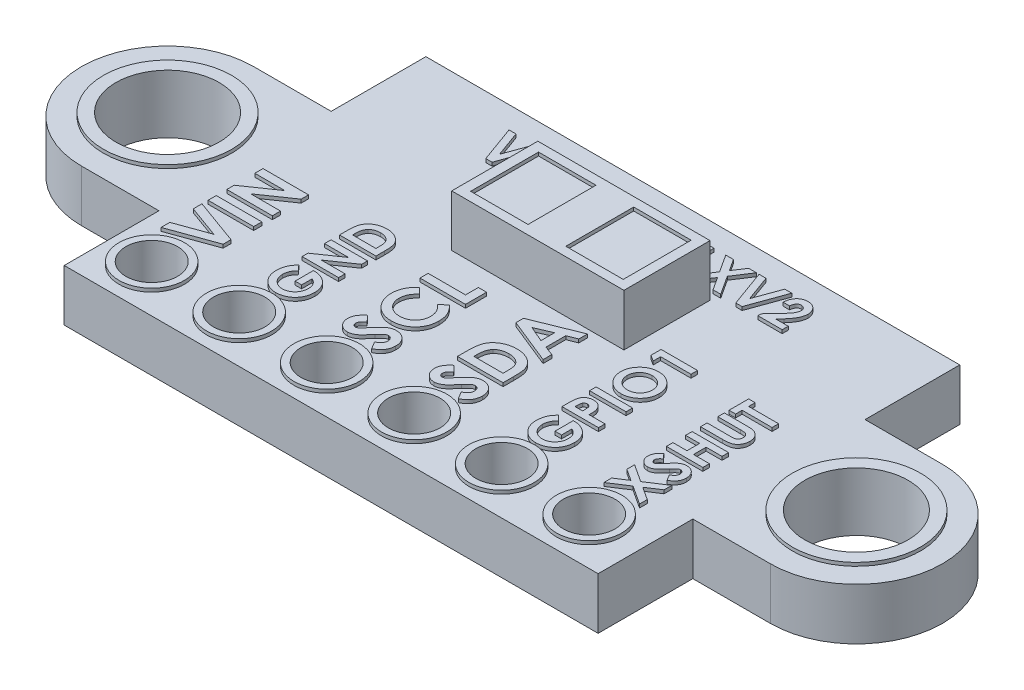
SolidWorks part; units mm, degrees
ref_plane "Ön Düzlem" through (0, 0, 0) normal (0, 0, 1) x (1, 0, 0)
ref_plane "Üst Düzlem" through (0, 0, 0) normal (0, 1, 0) x (1, 0, 0)
ref_plane "Sağ Düzlem" through (0, 0, 0) normal (1, 0, 0) x (0, 0, -1)
sketch "Çizim1" plane through (0, 0, 0) normal (0, 1, 0) x (1, 0, 0)
  line L0 (-10, 0) -> (10, 0) construction
  line L1 (-7.75, -5.25) -> (7.75, -5.25)
  line L2 (-7.75, -5.25) -> (-7.75, -2.5)
  line L3 (-7.75, 5.25) -> (7.75, 5.25)
  line L4 (7.75, -5.25) -> (7.75, -2.5)
  line L5 (-7.75, -5.25) -> (7.75, 5.25) construction
  line L6 (-7.75, 5.25) -> (7.75, -5.25) construction
  line L7 (-10, 2.5) -> (-7.75, 2.5)
  line L8 (-10, -2.5) -> (-7.75, -2.5)
  line L9 (10, -2.5) -> (7.75, -2.5)
  line L10 (10, 2.5) -> (7.75, 2.5)
  line L11 (-7.75, 2.5) -> (-7.75, 5.25)
  line L12 (7.75, 2.5) -> (7.75, 5.25)
  circle A0 centre (-10, 0) radius 1.5
  circle A1 centre (10, 0) radius 1.5
  arc A3 (-10, 2.5) -> (-10, -2.5) centre (-10, 0) ccw
  arc A4 (10, -2.5) -> (10, 2.5) centre (10, 0) ccw
  circle A5 centre (-10, 0) radius 2.5 construction
  circle A6 centre (10, 0) radius 2.5 construction
  point P0 (0, 0)
  dimension "D3" = 1
  dimension "D1" = 15.5
  dimension "D2" = 10.5
extrude "Yükseklik-Ekstrüzyon1" add sketch "Çizim1" along normal blind 1.5
sketch "Çizim2" plane through (0, 1.5, 0) normal (0, 1, 0) x (1, 0, 0)
  line L0 (0, 5.25) -> (0, 2) construction
  line L1 (7.75, 5.25) -> (-7.75, 5.25) construction
  line L3 (-2.5, 0.75) -> (2.5, 0.75)
  line L4 (-2.5, 0.75) -> (-2.5, 3.25)
  line L5 (-2.5, 3.25) -> (2.5, 3.25)
  line L6 (2.5, 0.75) -> (2.5, 3.25)
  line L7 (-2.5, 0.75) -> (2.5, 3.25) construction
  line L8 (-2.5, 3.25) -> (2.5, 0.75) construction
extrude "Yükseklik-Ekstrüzyon2" add sketch "Çizim2" along normal blind 1.5
sketch "Çizim3" plane through (0, 3, 0) normal (0, 1, 0) x (1, 0, 0)
  line L3 (0, 3.25) -> (0, 0.75) construction
  line L7 (2.5, 3.25) -> (-2.5, 3.25) construction
  line L12 (-2.5, 0.75) -> (2.5, 0.75) construction
  line L13 (0, 2) -> (-2.5, 2) construction
  line L14 (-2.5, 3.25) -> (-2.5, 0.75) construction
  line L15 (2.2157, 1.014) -> (0.548, 2.986) construction
  line L16 (-2.2157, 2.986) -> (-0.548, 2.986)
  line L17 (-2.2157, 2.986) -> (-2.2157, 1.014)
  line L18 (-2.2157, 1.014) -> (-0.548, 1.014)
  line L19 (-0.548, 2.986) -> (-0.548, 1.014)
  line L20 (-2.2157, 2.986) -> (-0.548, 1.014) construction
  line L21 (-2.2157, 1.014) -> (-0.548, 2.986) construction
  line L22 (2.2157, 2.986) -> (0.548, 1.014) construction
  line L23 (0.548, 2.986) -> (0.548, 1.014)
  line L24 (2.2157, 1.014) -> (0.548, 1.014)
  line L25 (2.2157, 2.986) -> (2.2157, 1.014)
  line L26 (2.2157, 2.986) -> (0.548, 2.986)
  point P10 (-1.3818, 2)
  point P19 (1.3818, 2)
extrude "Kes-Ekstrüzyon1" cut sketch "Çizim3" against normal blind 0.1
sketch "Çizim4" plane through (0, 1.5, 0) normal (0, 1, 0) x (1, 0, 0)
  line L0 (0, 0) -> (0, -1.1087) construction
  circle A0 centre (10, 0) radius 1.8604
  circle A1 centre (10, 0) radius 1.5 construction
  circle A2 centre (10, 0) radius 1.5
  circle A3 centre (-10, 0) radius 1.5
  circle A4 centre (-10, 0) radius 1.8604
extrude "Yükseklik-Ekstrüzyon3" add sketch "Çizim4" along normal blind 0.1 and the other way blind 1.6
sketch "Çizim5" plane through (0, 1.5, 0) normal (0, 1, 0) x (1, 0, 0)
  line L0 (-7.75, -5.25) -> (-7.75, -3.98) construction
  line L1 (-7.75, -2.5) -> (-7.75, -5.25) construction
  line L2 (-7.75, -3.98) -> (-6.48, -3.98) construction
  circle A0 centre (-6.48, -3.98) radius 0.75
  circle A1 centre (-3.94, -3.98) radius 0.75
  circle A2 centre (-1.4, -3.98) radius 0.75
  circle A3 centre (1.14, -3.98) radius 0.75
  circle A4 centre (3.68, -3.98) radius 0.75
  circle A5 centre (6.22, -3.98) radius 0.75
  dimension "D1" = 6
extrude "Kes-Ekstrüzyon2" cut sketch "Çizim5" against normal blind 3.1
sketch "Çizim6" plane through (0, 1.5, 0) normal (0, 1, 0) x (1, 0, 0)
  circle A0 centre (-6.48, -3.98) radius 0.75 construction
  circle A1 centre (-6.48, -3.98) radius 0.75
  circle A2 centre (-6.48, -3.98) radius 0.95
  dimension "D1" = 0.2
extrude "Yükseklik-Ekstrüzyon4" add sketch "Çizim6" along normal blind 0.1 and the other way blind 1.6
pattern_linear "LÇoğaltma1" count 6 spacing 2.54 along (1, 0, 0) of "Yükseklik-Ekstrüzyon4"
sketch "Çizim7" plane through (0, 1.5, 0) normal (0, 1, 0) x (1, 0, 0)
  line L0 (-3.3625, -3.03) -> (-3.3625, 1.2923) construction
  line L1 (-5.8779, -3.03) -> (-5.8779, 1.2923) construction
  line L2 (-0.8471, -3.03) -> (-0.8471, 1.2923) construction
  line L3 (1.6682, -3.03) -> (1.6682, 1.2923) construction
  line L4 (4.1836, -3.03) -> (4.1836, 1.2923) construction
  line L5 (6.6989, -3.03) -> (6.6989, 1.2923) construction
  text T0 "VIN" font "Century Gothic" height in points 5
  text T1 "GND" font "Century Gothic" height in points 4
  text T2 "<b>SCL</b>" font "Century Gothic" height in points 5
  text T3 "SDA" font "Century Gothic" height in points 5
  text T4 "GPIO1" font "Century Gothic" height in points 4
  text T5 "<b>XSHUT</b>" font "Century Gothic" height in points 4
  dimension "D1" = 6
extrude "Yükseklik-Ekstrüzyon5" add sketch "Çizim7" along normal blind 0.1
sketch "Çizim8" plane through (0, 1.5, 0) normal (0, 1, 0) x (1, 0, 0)
  line L0 (-5.0829, 3.4564) -> (4.9171, 3.4564) construction
  line L1 (0, 0) -> (0, 5.25) construction
  line L2 (7.75, 5.25) -> (-7.75, 5.25) construction
  text T0 "VL53L0/1XV2" font "Century Gothic" height in points 4
extrude "Yükseklik-Ekstrüzyon6" add sketch "Çizim8" along normal blind 0.1
sketch "Çizim9" plane through (0, 0, 0) normal (0, -1, 0) x (1, 0, 0)
  line L0 (-1.7136, -3.2806) -> (-1.2276, -3.2806)
  line L1 (2.6326, 0.7695) -> (3.9286, 0.7695)
  line L2 (2.6326, 0.7695) -> (2.6326, -2.0656)
  line L3 (2.6326, -2.0656) -> (3.9286, -2.0656)
  line L4 (3.9286, 0.7695) -> (3.9286, -2.0656)
  line L5 (2.6326, 0.7695) -> (3.9286, -2.0656) construction
  line L6 (2.6326, -2.0656) -> (3.9286, 0.7695) construction
  line L7 (-2.7136, -3.2806) -> (-2.2276, -3.2806)
  line L8 (-2.7136, -3.2806) -> (-2.7136, -4.3336)
  line L9 (-2.7136, -4.3336) -> (-2.2276, -4.3336)
  line L10 (-2.2276, -3.2806) -> (-2.2276, -4.3336)
  line L11 (-2.7136, -3.2806) -> (-2.2276, -4.3336) construction
  line L12 (-2.7136, -4.3336) -> (-2.2276, -3.2806) construction
  line L17 (-1.7136, -3.2806) -> (-1.7136, -4.3336)
  line L18 (-1.7136, -4.3336) -> (-1.2276, -4.3336)
  line L23 (-1.2276, -3.2806) -> (-1.2276, -4.3336)
  line L24 (-1.7136, -3.2806) -> (-1.2276, -4.3336) construction
  line L25 (-1.7136, -4.3336) -> (-1.2276, -3.2806) construction
  line L26 (-0.7136, -3.2806) -> (-0.2276, -3.2806)
  line L27 (-0.7136, -3.2806) -> (-0.7136, -4.3336)
  line L28 (-0.7136, -4.3336) -> (-0.2276, -4.3336)
  line L29 (-0.2276, -3.2806) -> (-0.2276, -4.3336)
  line L30 (-0.7136, -3.2806) -> (-0.2276, -4.3336) construction
  line L31 (-0.7136, -4.3336) -> (-0.2276, -3.2806) construction
  line L32 (-5.7336, 1.0241) -> (-5.2741, 1.0241)
  line L33 (-6.7336, 1.0241) -> (-6.2741, 1.0241)
  line L34 (-6.7336, 1.0241) -> (-6.7336, -0.1705)
  line L35 (-6.7336, -0.1705) -> (-6.2741, -0.1705)
  line L36 (-6.2741, 1.0241) -> (-6.2741, -0.1705)
  line L37 (-6.7336, 1.0241) -> (-6.2741, -0.1705) construction
  line L38 (-6.7336, -0.1705) -> (-6.2741, 1.0241) construction
  line L39 (-5.7336, 1.0241) -> (-5.7336, -0.1705)
  line L40 (-5.7336, -0.1705) -> (-5.2741, -0.1705)
  line L41 (-5.2741, 1.0241) -> (-5.2741, -0.1705)
  line L42 (-5.7336, 1.0241) -> (-5.2741, -0.1705) construction
  line L43 (-5.7336, -0.1705) -> (-5.2741, 1.0241) construction
  point P0 (3.2806, -0.648)
  point P5 (-2.4706, -3.8071)
  point P10 (-6.5038, 0.4268)
  point P11 (-1.4706, -3.8071)
  point P16 (-0.4706, -3.8071)
  point P27 (-5.5038, 0.4268)
  dimension "D1" = 3
  dimension "D2" = 2
extrude "Yükseklik-Ekstrüzyon7" add sketch "Çizim9" along normal blind 1
sketch "Çizim10" plane through (0, -1, 0) normal (0, -1, 0) x (1, 0, 0)
  line L0 (-0.2276, -4.3336) -> (-0.2276, -3.2806) construction
  line L1 (-0.2276, -3.2806) -> (-0.7136, -3.2806) construction
  line L2 (-0.7136, -3.2806) -> (-0.7136, -4.3336) construction
  line L3 (-0.7136, -4.3336) -> (-0.2276, -4.3336) construction
  line L4 (-5.2741, -0.1705) -> (-5.2741, 1.0241)
  line L5 (-5.2741, 1.0241) -> (-5.7336, 1.0241)
  line L6 (-5.7336, 1.0241) -> (-5.7336, -0.1705)
  line L7 (-5.7336, -0.1705) -> (-5.2741, -0.1705)
  line L8 (-5.2741, -0.1705) -> (-5.2741, 1.0241)
  line L9 (-5.2741, 1.0241) -> (-5.7336, 1.0241)
  line L10 (-5.7336, 1.0241) -> (-5.7336, -0.1705)
  line L11 (-5.7336, -0.1705) -> (-5.2741, -0.1705)
  line L12 (-6.2741, -0.1705) -> (-6.2741, 1.0241)
  line L13 (-6.2741, 1.0241) -> (-6.7336, 1.0241)
  line L14 (-6.7336, 1.0241) -> (-6.7336, -0.1705)
  line L15 (-6.7336, -0.1705) -> (-6.2741, -0.1705)
  line L16 (-6.2741, -0.1705) -> (-6.2741, 1.0241)
  line L17 (-6.2741, 1.0241) -> (-6.7336, 1.0241)
  line L18 (-6.7336, 1.0241) -> (-6.7336, -0.1705)
  line L19 (-6.7336, -0.1705) -> (-6.2741, -0.1705)
  line L20 (-1.2276, -4.3336) -> (-1.2276, -3.2806) construction
  line L21 (-1.2276, -3.2806) -> (-1.7136, -3.2806) construction
  line L22 (-1.7136, -3.2806) -> (-1.7136, -4.3336) construction
  line L23 (-1.7136, -4.3336) -> (-1.2276, -4.3336) construction
  line L24 (-2.2276, -4.3336) -> (-2.2276, -3.2806) construction
  line L25 (-2.2276, -3.2806) -> (-2.7136, -3.2806) construction
  line L26 (-2.7136, -3.2806) -> (-2.7136, -4.3336) construction
  line L27 (-2.7136, -4.3336) -> (-2.2276, -4.3336) construction
  line L28 (-0.2276, -4.3336) -> (-0.2276, -3.2806)
  line L29 (-0.2276, -3.2806) -> (-0.7136, -3.2806)
  line L30 (-0.7136, -3.2806) -> (-0.7136, -4.3336)
  line L31 (-0.7136, -4.3336) -> (-0.2276, -4.3336)
  line L32 (-1.2276, -4.3336) -> (-1.2276, -3.2806)
  line L33 (-1.2276, -3.2806) -> (-1.7136, -3.2806)
  line L34 (-1.7136, -3.2806) -> (-1.7136, -4.3336)
  line L35 (-1.7136, -4.3336) -> (-1.2276, -4.3336)
  line L36 (-2.2276, -4.3336) -> (-2.2276, -3.2806)
  line L37 (-2.2276, -3.2806) -> (-2.7136, -3.2806)
  line L38 (-2.7136, -3.2806) -> (-2.7136, -4.3336)
  line L39 (-2.7136, -4.3336) -> (-2.2276, -4.3336)
  dimension "D1" = 0
  dimension "D2" = 0
extrude "Kes-Ekstrüzyon3" cut sketch "Çizim10" against normal blind 0.5
